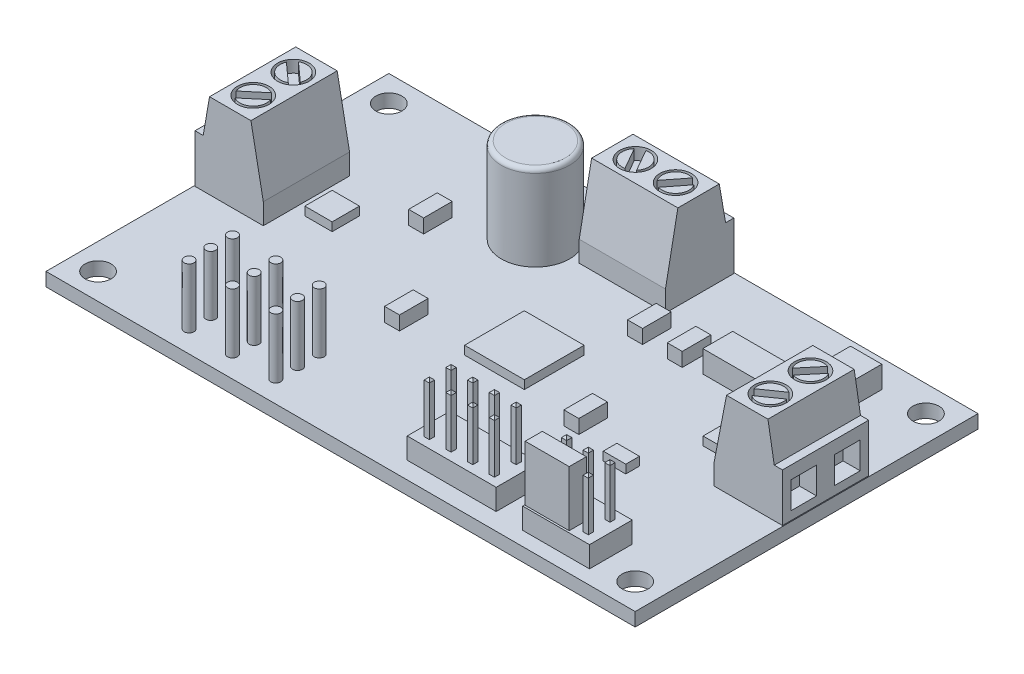
SolidWorks part; units mm, degrees
ref_plane "Front" through (0, 0, 0) normal (0, 0, 1) x (1, 0, 0)
ref_plane "Top" through (0, 0, 0) normal (0, 1, 0) x (1, 0, 0)
ref_plane "Right" through (0, 0, 0) normal (1, 0, 0) x (0, 0, -1)
sketch "Sketch1" plane through (0, 0, 0) normal (0, 1, 0) x (1, 0, 0)
  line L1 (0, 0) -> (69, 0)
  line L2 (0, 0) -> (0, 40.15)
  line L3 (0, 40.15) -> (69, 40.15)
  line L4 (69, 0) -> (69, 40.15)
  circle A0 centre (65.95, 37.1) radius 1.525
  circle A1 centre (3.05, 37.1) radius 1.525
  circle A2 centre (3.05, 3.05) radius 1.525
  circle A3 centre (65.95, 3.05) radius 1.525
  dimension "D3" = 3.05
  dimension "D4" = 3.05
  dimension "D5" = 3.05
  dimension "D6" = 3.05
  dimension "D1" = 69
  dimension "D2" = 40.15
  dimension "D7" = 3.05
  dimension "D8" = 3.05
  dimension "D9" = 3.05
  dimension "D10" = 3.05
extrude "Base-Extrude" add sketch "Sketch1" against normal blind 1.5748
sketch "Sketch2" plane through (0, 0, 0) normal (0, 1, 0) x (-1, 0, 0)
  line L0 (-69, 0) -> (-69, -40.15) construction
  line L1 (-68.9, -27.45) -> (-60.9, -27.45)
  line L2 (-0.1, -17.35) -> (-0.1, -27.45)
  line L3 (-68.9, -17.35) -> (-60.9, -17.35)
  line L4 (-60.9, -27.45) -> (-60.9, -17.35)
  line L5 (-69, -40.15) -> (0, -40.15) construction
  line L6 (-40.5, -40.05) -> (-30.4, -40.05)
  line L7 (-40.5, -40.05) -> (-40.5, -32.05)
  line L8 (-40.5, -32.05) -> (-30.4, -32.05)
  line L9 (-30.4, -40.05) -> (-30.4, -32.05)
  line L10 (0, -40.15) -> (0, 0) construction
  line L11 (-0.1, -27.45) -> (-8.1, -27.45)
  line L12 (-68.9, -17.35) -> (-68.9, -27.45)
  line L13 (-0.1, -17.35) -> (-8.1, -17.35)
  line L14 (-8.1, -27.45) -> (-8.1, -17.35)
  dimension "D1" = 12.7
  dimension "D2" = 10.1
  dimension "D3" = 10.1
  dimension "D4" = 10.1
  dimension "D5" = 0.1
  dimension "D6" = 0.1
  dimension "D7" = 8
  dimension "D8" = 12.7
  dimension "D9" = 28.5
  dimension "D10" = 0.1
  dimension "D11" = 8
  dimension "D12" = 8
extrude "Boss-Extrude1" add sketch "Sketch2" along normal blind 9.94
sketch "Sketch3" plane through (0, 0, -27.45) normal (0, 0, -1) x (-1, 0, 0)
  line L0 (-8.1, 9.94) -> (-8.1, 2.44)
  line L2 (-8.1, 9.94) -> (-8.1, 0) construction
  line L3 (-8.1, 9.94) -> (-0.1, 9.94) construction
  line L4 (-6.65, 9.94) -> (-8.1, 9.94)
  line L5 (-1.06, 5.64) -> (-1.8, 9.94)
  line L6 (-1.06, 5.64) -> (-0.1, 5.64)
  line L7 (-0.1, 9.94) -> (-0.1, 0) construction
  line L8 (-0.1, 5.64) -> (-0.1, 9.94)
  line L9 (-0.1, 9.94) -> (-1.8, 9.94)
  line L10 (-60.9, 9.94) -> (-60.9, 2.44)
  line L11 (-60.9, 9.94) -> (-60.9, 0) construction
  line L12 (-60.9, 9.94) -> (-62.35, 9.94)
  line L13 (-68.9, 9.94) -> (-60.9, 9.94) construction
  line L14 (-62.35, 9.94) -> (-60.9, 2.44)
  line L15 (-68.9, 9.94) -> (-68.9, 5.64)
  line L16 (-68.9, 9.94) -> (-68.9, 0) construction
  line L17 (-68.9, 5.64) -> (-67.94, 5.64)
  line L18 (-67.94, 5.64) -> (-67.2, 9.94)
  line L19 (-67.2, 9.94) -> (-68.9, 9.94)
  line L20 (-8.1, 2.44) -> (-6.65, 9.94)
  dimension "D1" = 4.3
  dimension "D2" = 0.96
  dimension "D3" = 1.7
  dimension "D4" = 7.5
  dimension "D5" = 1.45
  dimension "D6" = 1.45
  dimension "D7" = 7.5
  dimension "D8" = 0.96
  dimension "D9" = 1.7
  dimension "D10" = 4.3
extrude "Cut-Extrude1" cut sketch "Sketch3" against normal through all
sketch "Sketch4" plane through (40.5, 0, 0) normal (1, 0, 0) x (0, 0, -1)
  line L0 (40.05, 9.94) -> (40.05, 5.64)
  line L1 (40.05, 9.94) -> (38.35, 9.94)
  line L3 (32.05, 9.94) -> (40.05, 9.94) construction
  line L4 (40.05, 5.64) -> (39.09, 5.64)
  line L5 (38.35, 9.94) -> (39.09, 5.64)
  line L6 (32.05, 9.94) -> (32.05, 2.44)
  line L7 (32.05, 9.94) -> (32.05, 0) construction
  line L8 (32.05, 2.44) -> (33.5, 9.94)
  line L9 (33.5, 9.94) -> (32.05, 9.94)
  dimension "D1" = 0.96
  dimension "D2" = 4.3
  dimension "D3" = 1.7
  dimension "D4" = 1.45
  dimension "D5" = 7.5
extrude "Cut-Extrude2" cut sketch "Sketch4" against normal through all
sketch "Sketch5" plane through (0, 9.94, 0) normal (0, 1, 0) x (-1, 0, 0)
  line L0 (-67.2, -27.45) -> (-62.35, -27.45) construction
  line L1 (-62.35, -17.35) -> (-67.2, -17.35) construction
  line L2 (-67.2, -27.45) -> (-67.2, -17.35) construction
  line L3 (-40.5, -38.35) -> (-30.4, -38.35) construction
  line L4 (-40.5, -33.5) -> (-40.5, -38.35) construction
  line L5 (-30.4, -38.35) -> (-30.4, -33.5) construction
  line L6 (-6.65, -27.45) -> (-1.8, -27.45) construction
  line L7 (-1.8, -17.35) -> (-6.65, -17.35) construction
  line L8 (-1.8, -27.45) -> (-1.8, -17.35) construction
  circle A0 centre (-64.78, -20.05) radius 1.85
  circle A1 centre (-64.78, -24.75) radius 1.85
  circle A2 centre (-37.8, -35.93) radius 1.85
  circle A3 centre (-33.1, -35.93) radius 1.85
  circle A4 centre (-4.22, -24.75) radius 1.85
  circle A5 centre (-4.22, -20.05) radius 1.85
  dimension "D2" = 3.7
  dimension "D4" = 3.7
  dimension "D11" = 3.7
  dimension "D12" = 3.7
  dimension "D17" = 3.7
  dimension "D18" = 3.7
  dimension "D1" = 2.7
  dimension "D3" = 2.42
  dimension "D5" = 2.7
  dimension "D6" = 2.42
  dimension "D7" = 2.42
  dimension "D8" = 2.42
  dimension "D9" = 2.7
  dimension "D10" = 2.7
  dimension "D13" = 2.7
  dimension "D14" = 2.7
  dimension "D15" = 2.42
  dimension "D16" = 2.42
extrude "Cut-Extrude3" cut sketch "Sketch5" against normal blind 2
sketch "Sketch6" plane through (0, 9.94, 0) normal (0, 1, 0) x (-1, 0, 0)
  circle A0 centre (-64.78, -20.05) radius 1.55
  circle A1 centre (-64.78, -24.75) radius 1.55
  circle A2 centre (-37.8, -35.93) radius 1.55
  circle A3 centre (-33.1, -35.93) radius 1.55
  circle A4 centre (-4.22, -24.75) radius 1.55
  circle A5 centre (-4.22, -20.05) radius 1.55
  dimension "D1" = 3.1
  dimension "D2" = 3.1
  dimension "D3" = 3.1
  dimension "D4" = 3.1
  dimension "D5" = 3.1
  dimension "D6" = 3.1
extrude "Boss-Extrude4" add sketch "Sketch6" against normal up to next
sketch "Sketch7" plane through (0, 9.94, 0) normal (0, 1, 0) x (-1, 0, 0)
  line L0 (-65.7871, -21.3656) -> (-63.1993, -19.5536)
  line L1 (-66.3607, -20.5464) -> (-63.7729, -18.7344)
  line L2 (-65.393, -26.2584) -> (-63.401, -23.8844)
  line L3 (-66.159, -25.6156) -> (-64.167, -23.2416)
  line L4 (-62.35, -17.35) -> (-62.35, -27.45) construction
  arc A0 (-66.3607, -20.5464) -> (-65.7871, -21.3656) centre (-64.78, -20.05) ccw
  arc A1 (-63.1993, -19.5536) -> (-63.7729, -18.7344) centre (-64.78, -20.05) ccw
  arc A2 (-66.159, -25.6156) -> (-65.393, -26.2584) centre (-64.78, -24.75) ccw
  arc A3 (-63.401, -23.8844) -> (-64.167, -23.2416) centre (-64.78, -24.75) ccw
  point P6 (-64.78, -20.05)
  point P7 (-64.78, -24.75)
  dimension "D7" = 3.2564
  dimension "D8" = 3.3137
  dimension "D1" = 0.5
  dimension "D2" = 0.5
  dimension "D3" = 0.5
  dimension "D4" = 0.5
  dimension "D5" = 40
  dimension "D6" = 55
extrude "Cut-Extrude4" cut sketch "Sketch7" against normal blind 1.2
sketch "Sketch8" plane through (0, 9.94, 0) normal (0, 1, 0) x (-1, 0, 0)
  line L0 (-39.1699, -36.8712) -> (-37.2181, -34.3731)
  line L1 (-38.3819, -37.4869) -> (-36.4301, -34.9888)
  line L2 (-30.4, -33.5) -> (-40.5, -33.5) construction
  line L3 (-32.7399, -37.563) -> (-34.3276, -34.7944)
  line L4 (-31.8724, -37.0656) -> (-33.4601, -34.297)
  line L5 (-40.5, -38.35) -> (-30.4, -38.35) construction
  arc A0 (-39.1699, -36.8712) -> (-38.3819, -37.4869) centre (-37.8, -35.93) ccw
  arc A1 (-32.7399, -37.563) -> (-31.8724, -37.0656) centre (-33.1, -35.93) ccw
  arc A2 (-36.4301, -34.9888) -> (-37.2181, -34.3731) centre (-37.8, -35.93) ccw
  arc A3 (-33.4601, -34.297) -> (-34.3276, -34.7944) centre (-33.1, -35.93) ccw
  point P0 (-37.8, -35.93)
  point P1 (-33.1, -35.93)
  dimension "D1" = 3.3241
  dimension "D2" = 3.3445
  dimension "D3" = 0.5
  dimension "D4" = 1
  dimension "D5" = 128
  dimension "D6" = 0.5
  dimension "D7" = 1
  dimension "D8" = 60.168
extrude "Cut-Extrude5" cut sketch "Sketch8" against normal blind 1.2
sketch "Sketch10" plane through (0, 9.94, 0) normal (0, 1, 0) x (-1, 0, 0)
  line L0 (-3.3399, -26.2153) -> (-5.7692, -24.0279)
  line L1 (-2.6708, -25.4721) -> (-5.1001, -23.2847)
  line L2 (-3.3254, -18.6467) -> (-5.7573, -20.6873)
  line L3 (-2.6827, -19.4127) -> (-5.1146, -21.4533)
  line L4 (-1.8, -27.45) -> (-1.8, -17.35) construction
  arc A0 (-5.7573, -20.6873) -> (-5.1146, -21.4533) centre (-4.22, -20.05) ccw
  arc A1 (-3.3399, -26.2153) -> (-2.6708, -25.4721) centre (-4.22, -24.75) ccw
  arc A2 (-2.6827, -19.4127) -> (-3.3254, -18.6467) centre (-4.22, -20.05) ccw
  arc A3 (-5.1001, -23.2847) -> (-5.7692, -24.0279) centre (-4.22, -24.75) ccw
  point P0 (-4.22, -20.05)
  point P1 (-4.22, -24.75)
  dimension "D1" = 3.3284
  dimension "D2" = 3.4185
  dimension "D3" = 0.5
  dimension "D4" = 1
  dimension "D5" = 0.5
  dimension "D6" = 1
  dimension "D7" = 50
  dimension "D8" = 48
extrude "Cut-Extrude6" cut sketch "Sketch10" against normal blind 1.2
sketch "Sketch11" plane through (0, 0, -40.05) normal (0, 0, -1) x (-1, 0, 0)
  line L0 (-30.4, 5.64) -> (-30.4, 0) construction
  line L1 (-39.5, 1) -> (-36.5, 1)
  line L2 (-39.5, 1) -> (-39.5, 4.14)
  line L3 (-39.5, 4.14) -> (-36.5, 4.14)
  line L4 (-36.5, 1) -> (-36.5, 4.14)
  line L5 (-31.4, 1) -> (-34.4, 1)
  line L6 (-31.4, 1) -> (-31.4, 4.14)
  line L7 (-31.4, 4.14) -> (-34.4, 4.14)
  line L8 (-34.4, 1) -> (-34.4, 4.14)
  line L9 (-40.5, 5.64) -> (-40.5, 0) construction
  line L10 (-30.4, 5.64) -> (-40.5, 5.64) construction
  line L11 (-69, 0) -> (0, 0) construction
  dimension "D1" = 1
  dimension "D2" = 1
  dimension "D3" = 3
  dimension "D4" = 1.5
  dimension "D5" = 1.5
  dimension "D6" = 1
  dimension "D7" = 1
  dimension "D8" = 3
extrude "Cut-Extrude7" cut sketch "Sketch11" against normal blind 2
sketch "Sketch12" plane through (0.1, 0, 0) normal (-1, 0, 0) x (0, 0, 1)
  line L0 (-40.15, 0) -> (0, 0) construction
  line L1 (-26.45, 1) -> (-23.45, 1)
  line L2 (-26.45, 1) -> (-26.45, 4.14)
  line L3 (-26.45, 4.14) -> (-23.45, 4.14)
  line L4 (-23.45, 1) -> (-23.45, 4.14)
  line L5 (-18.35, 1) -> (-21.35, 1)
  line L6 (-18.35, 1) -> (-18.35, 4.14)
  line L7 (-18.35, 4.14) -> (-21.35, 4.14)
  line L8 (-21.35, 1) -> (-21.35, 4.14)
  line L9 (-17.35, 5.64) -> (-27.45, 5.64) construction
  line L10 (-17.35, 5.64) -> (-17.35, 0) construction
  line L11 (-27.45, 5.64) -> (-27.45, 0) construction
  dimension "D1" = 1
  dimension "D2" = 1
  dimension "D3" = 1.5
  dimension "D4" = 1.5
  dimension "D5" = 1
  dimension "D6" = 1
  dimension "D7" = 3
  dimension "D8" = 3
extrude "Cut-Extrude8" cut sketch "Sketch12" against normal blind 2
sketch "Sketch13" plane through (68.9, 0, 0) normal (1, 0, 0) x (0, 0, -1)
  line L0 (27.45, 5.64) -> (27.45, 0) construction
  line L1 (18.35, 1) -> (21.35, 1)
  line L2 (18.35, 1) -> (18.35, 4.14)
  line L3 (18.35, 4.14) -> (21.35, 4.14)
  line L4 (21.35, 1) -> (21.35, 4.14)
  line L5 (23.45, 4.14) -> (26.45, 4.14)
  line L6 (23.45, 4.14) -> (23.45, 1)
  line L7 (23.45, 1) -> (26.45, 1)
  line L8 (26.45, 4.14) -> (26.45, 1)
  line L9 (17.35, 5.64) -> (17.35, 0) construction
  line L10 (0, 0) -> (40.15, 0) construction
  line L11 (17.35, 5.64) -> (27.45, 5.64) construction
  dimension "D1" = 1
  dimension "D2" = 1
  dimension "D3" = 1
  dimension "D4" = 1
  dimension "D5" = 1.5
  dimension "D6" = 1.5
  dimension "D7" = 3
  dimension "D8" = 3
extrude "Cut-Extrude9" cut sketch "Sketch13" against normal blind 2
sketch "Sketch14" plane through (0, 0, 0) normal (0, 1, 0) x (-1, 0, 0)
  line L0 (-69, -40.15) -> (0, -40.15) construction
  line L1 (0, -40.15) -> (0, 0) construction
  circle A0 centre (-25.4, -31.92) radius 4
  dimension "D3" = 8
  dimension "D1" = 8.23
  dimension "D2" = 25.4
extrude "Boss-Extrude5" add sketch "Sketch14" along normal blind 10
fillet "Fillet1" radius 0.5
sketch "Sketch15" plane through (0, 0, 0) normal (0, 1, 0) x (-1, 0, 0)
  line L0 (-69, 0) -> (-69, -40.15) construction
  line L1 (-62, -6.65) -> (-54.18, -6.65)
  line L2 (-62, -6.65) -> (-62, -1.65)
  line L3 (-62, -1.65) -> (-54.18, -1.65)
  line L4 (-54.18, -6.65) -> (-54.18, -1.65)
  line L5 (0, 0) -> (-69, 0) construction
  line L7 (-50.72, -7) -> (-40.3, -7)
  line L8 (-50.72, -7) -> (-50.72, -2)
  line L9 (-50.72, -2) -> (-40.3, -2)
  line L10 (-40.3, -7) -> (-40.3, -2)
  dimension "D1" = 7.82
  dimension "D2" = 7
  dimension "D3" = 5
  dimension "D4" = 1.65
  dimension "D5" = 2
  dimension "D6" = 28.7
  dimension "D7" = 5
  dimension "D8" = 10.42
extrude "Boss-Extrude6" add sketch "Sketch15" along normal blind 2.46
sketch "Sketch16" plane through (0, 2.46, 0) normal (0, 1, 0) x (-1, 0, 0)
  line L0 (-54.18, -6.65) -> (-54.18, -1.65) construction
  line L1 (-60.935, -5.725) -> (-60.325, -5.725)
  line L2 (-60.935, -5.725) -> (-60.935, -5.115)
  line L3 (-60.935, -5.115) -> (-60.325, -5.115)
  line L4 (-60.325, -5.725) -> (-60.325, -5.115)
  line L5 (-60.935, -3.185) -> (-60.325, -3.185)
  line L6 (-60.935, -3.185) -> (-60.935, -2.575)
  line L7 (-60.935, -2.575) -> (-60.325, -2.575)
  line L8 (-60.325, -3.185) -> (-60.325, -2.575)
  line L9 (-58.395, -5.725) -> (-57.785, -5.725)
  line L10 (-58.395, -5.725) -> (-58.395, -5.115)
  line L11 (-58.395, -5.115) -> (-57.785, -5.115)
  line L12 (-57.785, -5.725) -> (-57.785, -5.115)
  line L13 (-58.395, -3.185) -> (-57.785, -3.185)
  line L14 (-58.395, -3.185) -> (-58.395, -2.575)
  line L15 (-58.395, -2.575) -> (-57.785, -2.575)
  line L16 (-57.785, -3.185) -> (-57.785, -2.575)
  line L17 (-55.855, -5.725) -> (-55.245, -5.725)
  line L18 (-55.855, -5.725) -> (-55.855, -5.115)
  line L19 (-55.855, -5.115) -> (-55.245, -5.115)
  line L20 (-55.245, -5.725) -> (-55.245, -5.115)
  line L21 (-55.855, -3.185) -> (-55.245, -3.185)
  line L22 (-55.855, -3.185) -> (-55.855, -2.575)
  line L23 (-55.855, -2.575) -> (-55.245, -2.575)
  line L24 (-55.245, -3.185) -> (-55.245, -2.575)
  line L25 (-62, -6.65) -> (-54.18, -6.65) construction
  line L26 (-50.72, -7) -> (-40.3, -7) construction
  line L27 (-49.6, -6.07) -> (-48.99, -6.07)
  line L28 (-49.6, -6.07) -> (-49.6, -5.46)
  line L29 (-49.6, -5.46) -> (-48.99, -5.46)
  line L30 (-48.99, -6.07) -> (-48.99, -5.46)
  line L31 (-49.6, -3.53) -> (-48.99, -3.53)
  line L32 (-49.6, -3.53) -> (-49.6, -2.92)
  line L33 (-49.6, -2.92) -> (-48.99, -2.92)
  line L34 (-48.99, -3.53) -> (-48.99, -2.92)
  line L35 (-47.06, -6.07) -> (-46.45, -6.07)
  line L36 (-47.06, -6.07) -> (-47.06, -5.46)
  line L37 (-47.06, -5.46) -> (-46.45, -5.46)
  line L38 (-46.45, -6.07) -> (-46.45, -5.46)
  line L39 (-47.06, -3.53) -> (-46.45, -3.53)
  line L40 (-47.06, -3.53) -> (-47.06, -2.92)
  line L41 (-47.06, -2.92) -> (-46.45, -2.92)
  line L42 (-46.45, -3.53) -> (-46.45, -2.92)
  line L43 (-44.52, -6.07) -> (-43.91, -6.07)
  line L44 (-44.52, -6.07) -> (-44.52, -5.46)
  line L45 (-44.52, -5.46) -> (-43.91, -5.46)
  line L46 (-43.91, -6.07) -> (-43.91, -5.46)
  line L47 (-44.52, -3.53) -> (-43.91, -3.53)
  line L48 (-44.52, -3.53) -> (-44.52, -2.92)
  line L49 (-44.52, -2.92) -> (-43.91, -2.92)
  line L50 (-43.91, -3.53) -> (-43.91, -2.92)
  line L51 (-41.98, -6.07) -> (-41.37, -6.07)
  line L52 (-41.98, -6.07) -> (-41.98, -5.46)
  line L53 (-41.98, -5.46) -> (-41.37, -5.46)
  line L54 (-41.37, -6.07) -> (-41.37, -5.46)
  line L55 (-41.98, -3.53) -> (-41.37, -3.53)
  line L56 (-41.98, -3.53) -> (-41.98, -2.92)
  line L57 (-41.98, -2.92) -> (-41.37, -2.92)
  line L58 (-41.37, -3.53) -> (-41.37, -2.92)
  line L59 (-40.3, -7) -> (-40.3, -2) construction
  dimension "D1" = 0.61
  dimension "D2" = 0.61
  dimension "D3" = 0.61
  dimension "D4" = 0.61
  dimension "D5" = 2.54
  dimension "D6" = 2.54
  dimension "D7" = 2.54
  dimension "D8" = 0.61
  dimension "D9" = 1.065
  dimension "D10" = 0.925
  dimension "D11" = 0.61
  dimension "D12" = 0.61
  dimension "D13" = 0.61
  dimension "D14" = 0.61
  dimension "D15" = 0.61
  dimension "D16" = 0.61
  dimension "D17" = 2.54
  dimension "D18" = 2.54
  dimension "D19" = 2.54
  dimension "D20" = 0.93
  dimension "D21" = 1.07
  dimension "D22" = 2.54
extrude "Boss-Extrude7" add sketch "Sketch16" along normal blind 6
chamfer "Chamfer2" distance 0.25 angle 45
sketch "Sketch17" plane through (0, -1.5748, 0) normal (0, -1, 0) x (1, 0, 0)
  line L0 (69, 0) -> (69, -40.15) construction
  line L1 (60.17, -10.93) -> (51.47, -10.93)
  line L2 (60.17, -10.93) -> (60.17, -20.47)
  line L3 (60.17, -20.47) -> (51.47, -20.47)
  line L4 (51.47, -10.93) -> (51.47, -20.47)
  line L5 (60.17, -23.99) -> (51.47, -23.99)
  line L6 (60.17, -23.99) -> (60.17, -33.53)
  line L7 (60.17, -33.53) -> (51.47, -33.53)
  line L8 (51.47, -23.99) -> (51.47, -33.53)
  line L9 (0, 0) -> (69, 0) construction
  line L10 (69, -40.15) -> (0, -40.15) construction
  line L11 (0, -40.15) -> (0, 0) construction
  line L12 (16.36, -10.93) -> (7.66, -10.93)
  line L13 (16.36, -10.93) -> (16.36, -20.47)
  line L14 (16.36, -20.47) -> (7.66, -20.47)
  line L15 (7.66, -10.93) -> (7.66, -20.47)
  line L16 (16.36, -23.99) -> (7.66, -23.99)
  line L17 (16.36, -23.99) -> (16.36, -33.53)
  line L18 (16.36, -33.53) -> (7.66, -33.53)
  line L19 (7.66, -23.99) -> (7.66, -33.53)
  dimension "D1" = 8.83
  dimension "D2" = 10.93
  dimension "D3" = 9.54
  dimension "D4" = 9.54
  dimension "D5" = 8.7
  dimension "D6" = 8.7
  dimension "D7" = 6.62
  dimension "D8" = 7.66
  dimension "D9" = 8.7
extrude "Boss-Extrude8" add sketch "Sketch17" along normal blind 4.35
sketch "Sketch19" plane through (0, 0, 0) normal (0, 1, 0) x (-1, 0, 0)
  line L1 (-60.93, -36.95) -> (-57.27, -36.95)
  line L2 (-60.93, -36.95) -> (-60.93, -32.75)
  line L3 (-60.93, -32.75) -> (-57.27, -32.75)
  line L4 (-57.27, -36.95) -> (-57.27, -32.75)
  line L5 (-55.4, -31.55) -> (-48.87, -31.55)
  line L6 (-55.4, -31.55) -> (-55.4, -28.05)
  line L7 (-55.4, -28.05) -> (-48.87, -28.05)
  line L8 (-48.87, -31.55) -> (-48.87, -28.05)
  line L10 (-69, 0) -> (-69, -40.15) construction
  line L11 (-69, -40.15) -> (0, -40.15) construction
  dimension "D1" = 8.07
  dimension "D2" = 3.66
  dimension "D3" = 4.2
  dimension "D4" = 3.2
  dimension "D5" = 13.6
  dimension "D6" = 6.53
  dimension "D7" = 8.6
  dimension "D8" = 3.5
extrude "Boss-Extrude9" add sketch "Sketch19" along normal blind 2.58
sketch "Sketch20" plane through (0, 0, 0) normal (0, 1, 0) x (-1, 0, 0)
  line L0 (0, 0) -> (-69, 0) construction
  line L1 (-40, -23.02) -> (-33, -23.02)
  line L2 (-40, -23.02) -> (-40, -16.02)
  line L3 (-40, -16.02) -> (-33, -16.02)
  line L4 (-33, -23.02) -> (-33, -16.02)
  line L5 (0, -40.15) -> (0, 0) construction
  dimension "D1" = 16.02
  dimension "D2" = 7
  dimension "D3" = 7
  dimension "D4" = 33
extrude "Boss-Extrude10" add sketch "Sketch20" along normal blind 1
sketch "Sketch21" plane through (0, 0, 0) normal (0, 1, 0) x (-1, 0, 0)
  line L0 (0, 0) -> (-69, 0) construction
  line L1 (0, -40.15) -> (0, 0) construction
  circle A0 centre (-14.22, -2.54) radius 0.575
  circle A1 centre (-19.3, -2.54) radius 0.575
  circle A2 centre (-24.38, -2.54) radius 0.575
  dimension "D1" = 1.15
  dimension "D2" = 1.15
  dimension "D3" = 1.15
  dimension "D4" = 5.08
  dimension "D5" = 5.08
  dimension "D6" = 2.54
  dimension "D7" = 14.22
extrude "Boss-Extrude11" add sketch "Sketch21" along normal blind 7
sketch "Sketch22" plane through (0, 0, 0) normal (0, 1, 0) x (-1, 0, 0)
  circle A0 centre (-14.22, -5.08) radius 0.575
  circle A1 centre (-19.3, -5.08) radius 0.575
  circle A2 centre (-24.38, -5.08) radius 0.575
  point P6 (-14.22, -2.54)
  point P7 (-19.3, -2.54)
  point P9 (-24.38, -2.54)
  dimension "D1" = 1.15
  dimension "D2" = 1.15
  dimension "D3" = 1.15
  dimension "D4" = 2.54
extrude "Boss-Extrude12" add sketch "Sketch22" along normal blind 7
sketch "Sketch23" plane through (0, 0, 0) normal (0, 1, 0) x (-1, 0, 0)
  circle A0 centre (-24.38, -7.62) radius 0.575
  circle A1 centre (-19.3, -7.62) radius 0.575
  circle A2 centre (-14.22, -7.62) radius 0.575
  point P6 (-19.3, -5.08)
  point P7 (-24.38, -5.08)
  point P9 (-14.22, -5.08)
  dimension "D1" = 1.15
  dimension "D2" = 1.15
  dimension "D3" = 1.15
  dimension "D4" = 2.54
extrude "Boss-Extrude13" add sketch "Sketch23" along normal blind 7
sketch "Sketch24" plane through (0, 0, 0) normal (0, 1, 0) x (-1, 0, 0)
  line L0 (-68.9, -17.35) -> (-68.9, -27.45) construction
  line L1 (-59.37, -23.98) -> (-56.17, -23.98)
  line L2 (-59.37, -23.98) -> (-59.37, -20.78)
  line L3 (-59.37, -20.78) -> (-56.17, -20.78)
  line L4 (-56.17, -23.98) -> (-56.17, -20.78)
  line L5 (-12.73, -23.98) -> (-9.53, -23.98)
  line L6 (-12.73, -23.98) -> (-12.73, -20.78)
  line L7 (-12.73, -20.78) -> (-9.53, -20.78)
  line L8 (-9.53, -23.98) -> (-9.53, -20.78)
  line L9 (0, -40.15) -> (0, 0) construction
  line L10 (-69, -40.15) -> (0, -40.15) construction
  line L11 (0, 0) -> (-69, 0) construction
  line L12 (-54.5, -15) -> (-51.86, -15)
  line L13 (-54.5, -15) -> (-54.5, -13.4)
  line L14 (-54.5, -13.4) -> (-51.86, -13.4)
  line L15 (-51.86, -15) -> (-51.86, -13.4)
  line L16 (-69, 0) -> (-69, -40.15) construction
  dimension "D1" = 12.73
  dimension "D2" = 12.73
  dimension "D3" = 16.17
  dimension "D4" = 16.17
  dimension "D5" = 3.2
  dimension "D6" = 3.2
  dimension "D7" = 3.2
  dimension "D8" = 3.2
  dimension "D9" = 15
  dimension "D10" = 14.5
  dimension "D11" = 1.6
  dimension "D12" = 2.64
extrude "Boss-Extrude14" add sketch "Sketch24" along normal blind 1
sketch "Sketch25" plane through (0, 0, 0) normal (0, 1, 0) x (-1, 0, 0)
  line L0 (-69, 0) -> (-69, -40.15) construction
  line L1 (-47, -30.86) -> (-45.25, -30.86)
  line L2 (-47, -30.86) -> (-47, -27.51)
  line L3 (-47, -27.51) -> (-45.25, -27.51)
  line L4 (-45.25, -30.86) -> (-45.25, -27.51)
  line L5 (-42.35, -30.86) -> (-40.6, -30.86)
  line L6 (-42.35, -30.86) -> (-42.35, -27.51)
  line L7 (-42.35, -27.51) -> (-40.6, -27.51)
  line L8 (-40.6, -30.86) -> (-40.6, -27.51)
  line L9 (-69, -40.15) -> (0, -40.15) construction
  line L10 (0, -40.15) -> (0, 0) construction
  line L11 (-47.75, -18) -> (-46, -18)
  line L12 (-47.75, -18) -> (-47.75, -14.65)
  line L13 (-47.75, -14.65) -> (-46, -14.65)
  line L14 (-46, -18) -> (-46, -14.65)
  line L15 (-26.75, -18) -> (-25, -18)
  line L16 (-26.75, -18) -> (-26.75, -14.65)
  line L17 (-26.75, -14.65) -> (-25, -14.65)
  line L18 (-25, -18) -> (-25, -14.65)
  line L19 (-18.32, -29.25) -> (-16.57, -29.25)
  line L20 (-18.32, -29.25) -> (-18.32, -25.9)
  line L21 (-18.32, -25.9) -> (-16.57, -25.9)
  line L22 (-16.57, -29.25) -> (-16.57, -25.9)
  dimension "D1" = 22
  dimension "D2" = 1.75
  dimension "D3" = 1.75
  dimension "D4" = 3.35
  dimension "D5" = 3.35
  dimension "D6" = 9.29
  dimension "D7" = 9.29
  dimension "D8" = 28.4
  dimension "D9" = 23
  dimension "D10" = 1.75
  dimension "D11" = 3.35
  dimension "D12" = 22.15
  dimension "D13" = 3.35
  dimension "D14" = 3.35
  dimension "D15" = 1.75
  dimension "D16" = 1.75
  dimension "D17" = 25
  dimension "D18" = 16.57
  dimension "D19" = 10.9
extrude "Boss-Extrude15" add sketch "Sketch25" along normal blind 1.63
sketch "Sketch26" plane through (0, 2.46, 0) normal (0, 1, 0) x (-1, 0, 0)
  line L0 (-58.395, -3.185) -> (-58.395, -2.575) construction
  line L1 (-59.395, -3.885) -> (-54.245, -3.885)
  line L2 (-59.395, -3.885) -> (-59.395, -1.875)
  line L3 (-59.395, -1.875) -> (-54.245, -1.875)
  line L4 (-54.245, -3.885) -> (-54.245, -1.875)
  line L5 (-55.245, -2.575) -> (-55.245, -3.185) construction
  line L6 (-58.395, -2.575) -> (-57.785, -2.575) construction
  line L7 (-55.245, -3.185) -> (-55.855, -3.185) construction
  dimension "D1" = 1
  dimension "D2" = 0.7
  dimension "D3" = 2.01
  dimension "D4" = 1
  dimension "D5" = 0.7
extrude "Boss-Extrude16" add sketch "Sketch26" along normal blind 6.5
